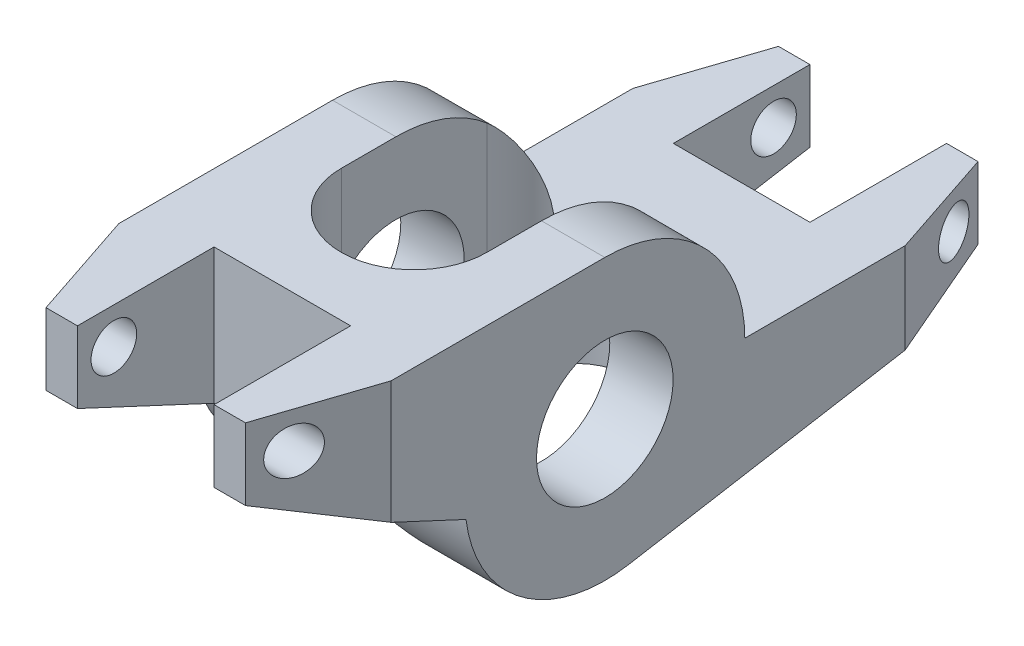
SolidWorks part; units mm, degrees
ref_plane "Front Plane" through (0, 0, 0) normal (0, 0, 1) x (1, 0, 0)
ref_plane "Top Plane" through (0, 0, 0) normal (0, 1, 0) x (1, 0, 0)
ref_plane "Right Plane" through (0, 0, 0) normal (1, 0, 0) x (0, 0, -1)
sketch "Sketch1" plane through (0, 0, 0) normal (1, 0, 0) x (0, 0, -1)
  line L0 (0, 9.765) -> (-22.53, 9.765)
  line L1 (-22.53, 9.765) -> (-22.53, 4.765)
  line L2 (-22.53, 4.765) -> (-9.6881, -1.2233)
  line L3 (9.765, 0) -> (28.575, 0)
  line L4 (28.575, 0) -> (28.575, -5)
  line L5 (28.575, -5) -> (1.653, -9.6241)
  circle A0 centre (0, 0) radius 4.765
  arc A1 (-9.6881, -1.2233) -> (1.653, -9.6241) centre (0, 0) ccw
  circle A2 centre (0, 0) radius 9.765 construction
  arc A3 (9.765, 0) -> (0, 9.765) centre (0, 0) ccw
  dimension "D1" = 9.53
  dimension "D3" = 22.53
  dimension "D4" = 5
  dimension "D5" = 25
  dimension "D6" = 28.575
  dimension "D7" = 5
  dimension "D2" = 5
extrude "Boss-Extrude1" add sketch "Sketch1" along normal mid plane 19
chamfer "Chamfer1" distance 2.54 distance2 7.62 2 edges at (9.5, 7.265, 22.53) (9.5, -2.5, -28.575)
chamfer "Chamfer2" distance 7.62 distance2 2.54 2 edges at (-9.5, 7.265, 22.53) (-9.5, -2.5, -28.575)
sketch "Sketch2" plane through (0, 0, 0) normal (0, 1, 0) x (1, 0, 0)
  line L0 (0, 6.35) -> (0, -3.81) construction
  line L1 (5.08, 6.35) -> (5.08, -3.81)
  line L2 (-5.08, 6.35) -> (-5.08, -3.81)
  arc A0 (5.08, 6.35) -> (-5.08, 6.35) centre (0, 6.35) ccw
  arc A1 (-5.08, -3.81) -> (5.08, -3.81) centre (0, -3.81) ccw
  point P3 (0, 1.27)
  dimension "D1" = 10.16
  dimension "D2" = 10.16
  dimension "D3" = 3.81
extrude "Cut-Extrude1" cut sketch "Sketch2" against normal mid plane 34
sketch "Sketch3" plane through (0, 0, 0) normal (0, 1, 0) x (1, 0, 0)
  line L0 (6.96, 28.575) -> (-6.96, 28.575) construction
  line L1 (-4.765, 19.045) -> (4.765, 19.045)
  line L2 (-4.765, 19.045) -> (-4.765, 28.575)
  line L3 (-4.765, 28.575) -> (4.765, 28.575)
  line L4 (4.765, 19.045) -> (4.765, 28.575)
  line L5 (-4.765, 19.045) -> (4.765, 28.575) construction
  line L6 (-4.765, 28.575) -> (4.765, 19.045) construction
  line L7 (6.96, -22.53) -> (-6.96, -22.53) construction
  line L8 (-4.765, -13) -> (4.765, -13)
  line L9 (-4.765, -13) -> (-4.765, -22.53)
  line L10 (-4.765, -22.53) -> (4.765, -22.53)
  line L11 (4.765, -13) -> (4.765, -22.53)
  line L12 (-4.765, -13) -> (4.765, -22.53) construction
  line L13 (-4.765, -22.53) -> (4.765, -13) construction
  point P0 (0, 23.81)
  point P7 (0, -17.765)
  point P14 (0, 0)
  dimension "D1" = 9.53
  dimension "D2" = 9.53
  dimension "D3" = 9.53
  dimension "D4" = 9.53
extrude "Cut-Extrude2" cut sketch "Sketch3" against normal mid plane 34
sketch "Sketch4" plane through (0, 0, 0) normal (1, 0, 0) x (0, 0, -1)
  line L0 (20.955, 0) -> (28.575, 0) construction
  line L1 (28.575, 0) -> (28.575, -5) construction
  line L2 (-22.53, 9.765) -> (-14.91, 9.765) construction
  line L3 (-22.53, 4.765) -> (-22.53, 9.765) construction
  circle A0 centre (26.035, -2.54) radius 1.59
  circle A1 centre (-19.99, 7.225) radius 1.59
  dimension "D1" = 3.18
  dimension "D4" = 2.54
  dimension "D2" = 2.54
  dimension "D3" = 2.54
  dimension "D5" = 2.54
extrude "Cut-Extrude3" cut sketch "Sketch4" against normal mid plane 34
